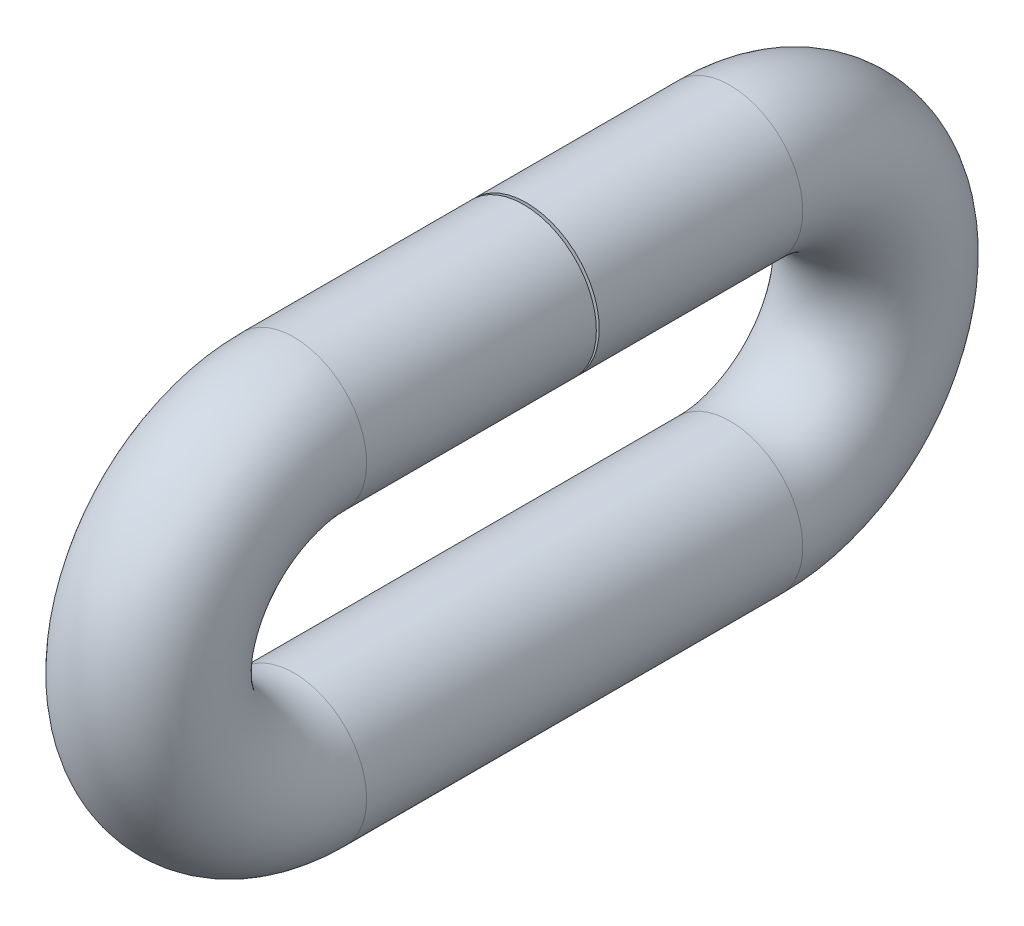
SolidWorks part; units mm, degrees
material "ASTM A36 Steel"
ref_plane "Front Plane" through (0, 0, 0) normal (0, 0, 1) x (1, 0, 0)
ref_plane "Top Plane" through (0, 0, 0) normal (0, 1, 0) x (1, 0, 0)
ref_plane "Right Plane" through (0, 0, 0) normal (1, 0, 0) x (0, 0, -1)
sketch "Sketch1" plane through (0, 0, 0) normal (0, 0, 1) x (1, 0, 0)
  circle A0 centre (0, 0) radius 63.5
  dimension "D1" = 127
sketch "Sketch2" plane through (0, 0, 0) normal (1, 0, 0) x (0, 0, -1)
  line L0 (0, 0) -> (177.8, 0)
  line L1 (-203.2, -254) -> (177.8, -254)
  line L2 (-203.2, 0) -> (-2.54, 0)
  arc A0 (177.8, 0) -> (177.8, -254) centre (177.8, -127) cw
  arc A1 (-203.2, -254) -> (-203.2, 0) centre (-203.2, -127) cw
  dimension "D2" = 127
  dimension "D3" = 127
  dimension "D1" = 2.54
  dimension "D4" = 381
  dimension "D5" = 177.8
sweep "Sweep1" add profiles "Sketch1" path "Sketch2"
